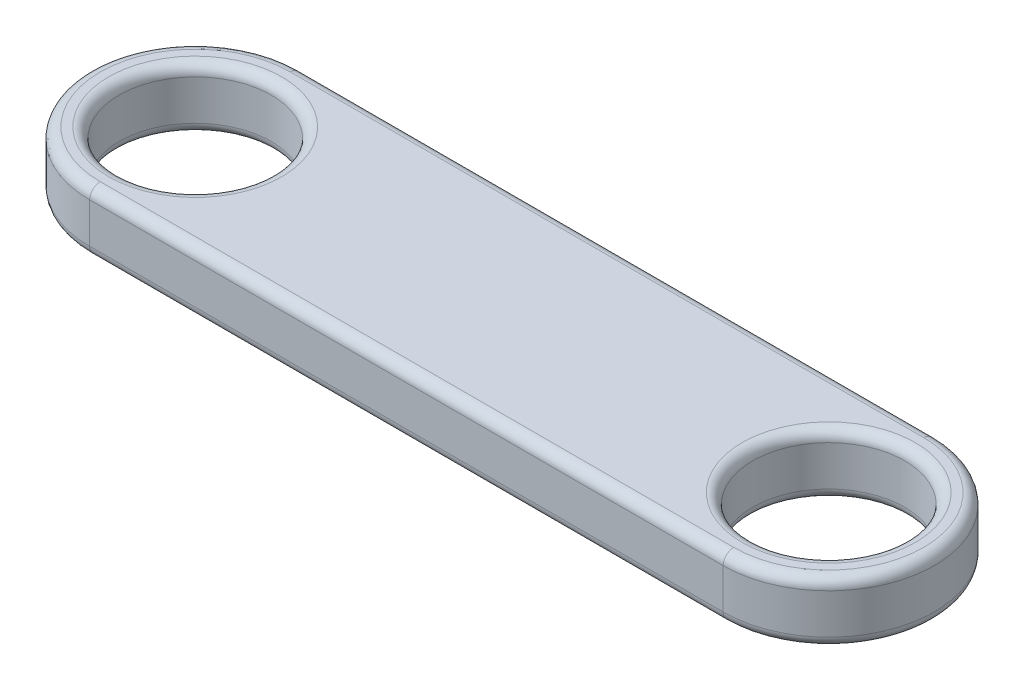
SolidWorks part; units mm, degrees
ref_plane "Front Plane" through (0, 0, 0) normal (0, 0, 1) x (1, 0, 0)
ref_plane "Top Plane" through (0, 0, 0) normal (0, 1, 0) x (1, 0, 0)
ref_plane "Right Plane" through (0, 0, 0) normal (1, 0, 0) x (0, 0, -1)
sketch "Sketch1" plane through (0, 0, 0) normal (0, 1, 0) x (1, 0, 0)
  line L0 (0, 5) -> (30, 5)
  line L1 (0, -5) -> (30, -5)
  circle A0 centre (0, 0) radius 3.6
  circle A1 centre (30, 0) radius 3.6
  circle A2 centre (0, 0) radius 5 construction
  circle A3 centre (30, 0) radius 5 construction
  arc A4 (0, 5) -> (0, -5) centre (0, 0) ccw
  arc A5 (30, 5) -> (30, -5) centre (30, 0) cw
  dimension "D2" = 7.2
  dimension "D3" = 10
  dimension "D1" = 30
extrude "Boss-Extrude1" add sketch "Sketch1" along normal blind 2.9
fillet "Fillet1" radius 0.5 12 edges at (-5, 0, 0) (15, 0, -5) (35, 0, 0) (-5, 2.9, 0) (15, 2.9, -5) (35, 2.9, 0) (15, 0, 5) (15, 2.9, 5) (30, 2.9, 3.6) (30, 0, 3.6) (0, 2.9, 3.6) (0, 0, 3.6)
equation "\"Bearing Inner Diameter\"= 3.1mm"
equation "\"Bearing Outer Diameter\" = 7.25mm"
equation "\"ArmLength\" = 25mm"
equation "\"ArmLength2\" = 30mm"
equation "\"D1@Sketch1\"=\"ArmLength2\""
